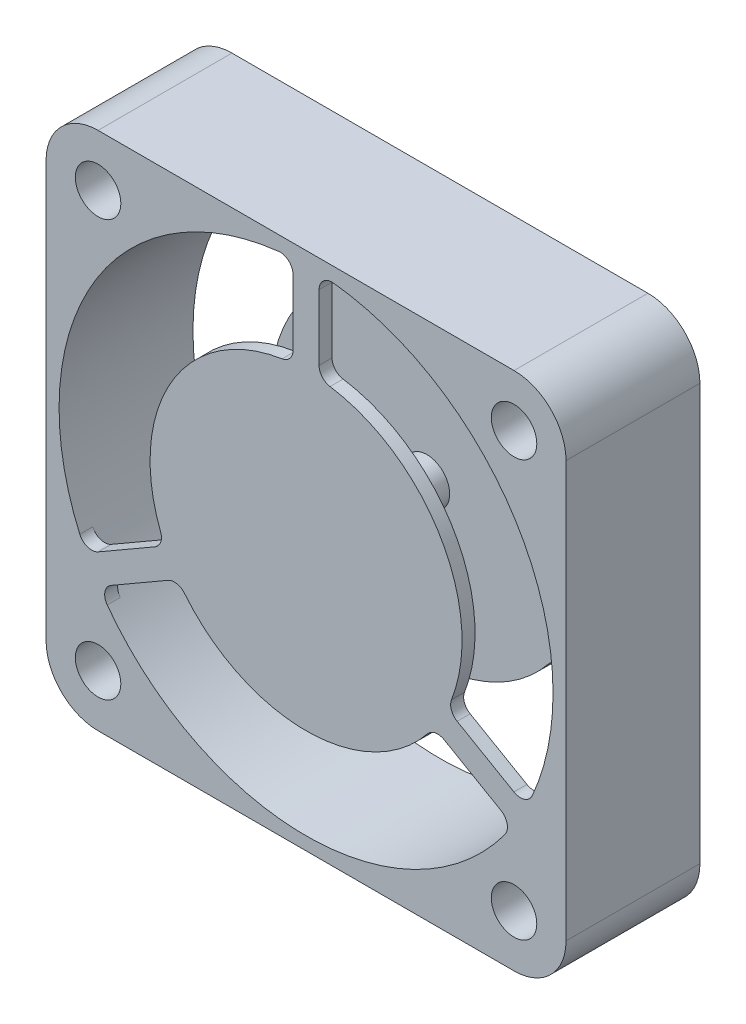
SolidWorks part; units mm, degrees
ref_plane "Front Plane" through (0, 0, 0) normal (0, 0, 1) x (1, 0, 0)
ref_plane "Top Plane" through (0, 0, 0) normal (0, 1, 0) x (1, 0, 0)
ref_plane "Right Plane" through (0, 0, 0) normal (1, 0, 0) x (0, 0, -1)
sketch "Sketch1" plane through (0, 0, 0) normal (0, 0, 1) x (1, 0, 0)
  line L1 (0, -4) -> (32, -4)
  line L2 (-4, 0) -> (-4, 32)
  line L3 (0, 36) -> (32, 36)
  line L4 (36, 0) -> (36, 32)
  arc A0 (-4, 0) -> (0, -4) centre (0, 0) ccw
  arc A1 (0, 36) -> (-4, 32) centre (0, 32) ccw
  arc A2 (36, 32) -> (32, 36) centre (32, 32) ccw
  arc A3 (32, -4) -> (36, 0) centre (32, 0) ccw
  dimension "D2" = 32
  dimension "D3" = 4
  dimension "D4" = 4
  dimension "D5" = 4
  dimension "D6" = 4
  dimension "D7" = 4
  dimension "D8" = 4
  dimension "D9" = 4
  dimension "D10" = 4
  dimension "D11" = 32
extrude "Boss-Extrude1" add sketch "Sketch1" along normal blind 10.3
sketch "Sketch2" plane through (0, 0, 10.3) normal (0, 0, 1) x (1, 0, 0)
  circle A0 centre (0, 0) radius 1.75
  circle A1 centre (0, 32) radius 1.75
  circle A2 centre (32, 0) radius 1.75
  circle A3 centre (32, 32) radius 1.75
  dimension "D1" = 3.5
  dimension "D2" = 3.5
  dimension "D3" = 3.5
  dimension "D4" = 3.5
extrude "Cut-Extrude1" cut sketch "Sketch2" against normal through all
sketch "Sketch3" plane through (0, 0, 10.3) normal (0, 0, 1) x (1, 0, 0)
  line L0 (32, 36) -> (0, 36) construction
  line L1 (-4, 32) -> (-4, 0) construction
  circle A0 centre (16, 16) radius 19
  circle A1 centre (16, 16) radius 12
  point P4 (16, 36)
  point P7 (-4, 16)
  dimension "D1" = 38
  dimension "D2" = 24
extrude "Cut-Extrude2" cut sketch "Sketch3" against normal through all
sketch "Sketch4" plane through (0, 0, 0) normal (0, 0, 1) x (1, 0, 0)
  line L0 (15, 27.9583) -> (15, 34.9737)
  line L1 (17, 34.9737) -> (17, 27.9583)
  line L2 (16, 16) -> (16, 41.3326) construction
  circle A0 centre (16, 16) radius 12 construction
  circle A1 centre (16, 16) radius 19 construction
  arc A2 (17, 27.9583) -> (15, 27.9583) centre (16, 16) ccw
  arc A3 (17, 34.9737) -> (15, 34.9737) centre (16, 16) ccw
  point P8 (16, 28)
  dimension "D1" = 2
extrude "Boss-Extrude2" add sketch "Sketch4" along normal up to surface (10.3 mm away) up to face at (28, 16, 10.3)
pattern_circular "CirPattern1" count 3 every 120 about axis through (16, 16, 0) along (0, 0, 1) of "Boss-Extrude2"
fillet "Fillet2" radius 1 12 edges at (-0.9317, 7.3792, 5.15) (5.1438, 10.8869, 5.15) (0.0683, 5.6471, 5.15) (31.9317, 5.6471, 5.15) (6.1438, 9.1548, 5.15) (25.8562, 9.1548, 5.15) (32.9317, 7.3792, 5.15) (26.8562, 10.8869, 5.15) (17, 27.9583, 5.15) (15, 34.9737, 5.15) (15, 27.9583, 5.15) (17, 34.9737, 5.15)
sketch "Sketch5" plane through (0, 0, 0) normal (0, 0, 1) x (1, 0, 0)
  circle A0 centre (16, 16) radius 19
  arc A1 (33.4082, 8.3871) -> (18.1111, 34.8824) centre (16, 16) ccw construction
extrude "Cut-Extrude3" cut sketch "Sketch5" along normal offset from surface (8.3 mm away) 1 from offset 1 up to face at (16, 5.5768, 10.3)
sketch "Sketch6" plane through (0, 0, 1) normal (0, 0, 1) x (1, 0, 0)
  circle A0 centre (16, 16) radius 1.75
  dimension "D1" = 3.5
extrude "Boss-Extrude3" add sketch "Sketch6" along normal up to surface (8.3 mm away) up to face at (16, 16, 9.3)
